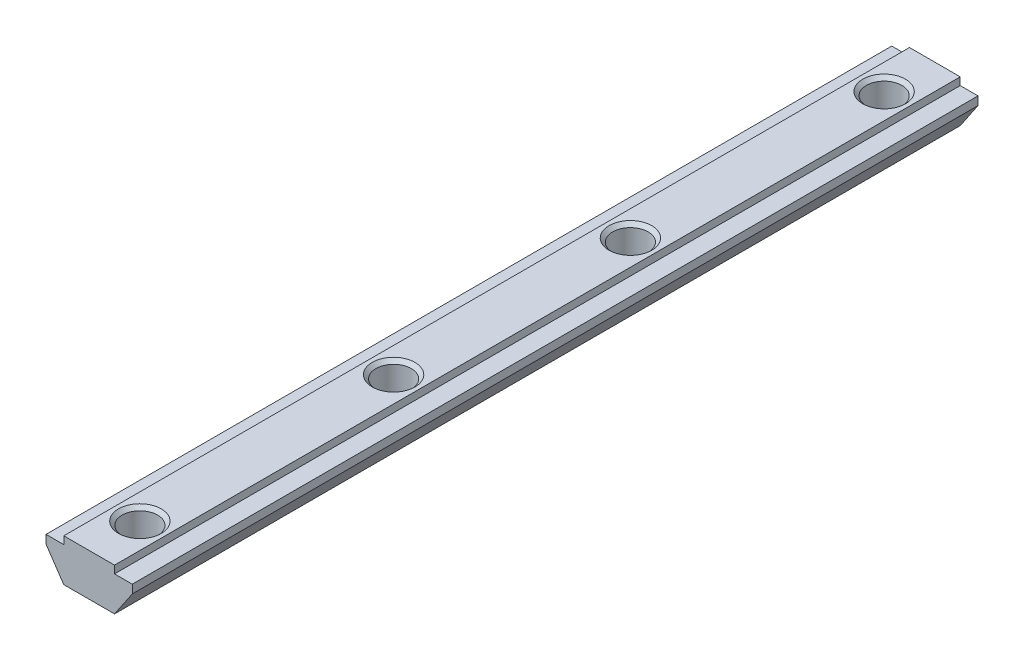
SolidWorks part; units mm, degrees
ref_plane "Спереди" through (0, 0, 0) normal (0, 0, 1) x (1, 0, 0)
ref_plane "Сверху" through (0, 0, 0) normal (0, 1, 0) x (1, 0, 0)
ref_plane "Справа" through (0, 0, 0) normal (1, 0, 0) x (0, 0, -1)
sketch "Эскиз1" plane through (0, 0, 0) normal (0, 0, 1) x (1, 0, 0)
  line L0 (3, 0) -> (-3, 0)
  line L1 (-3, 0) -> (-3, -0.9)
  line L2 (-3, -0.9) -> (-5.1, -0.9)
  line L3 (-5.1, -0.9) -> (-5.1, -1.9)
  line L4 (-5.1, -1.9) -> (-3, -5)
  line L5 (-3, -5) -> (3, -5)
  line L6 (0, -5) -> (0, 0) construction
  line L7 (5.1, -1.9) -> (3, -5)
  line L8 (5.1, -0.9) -> (5.1, -1.9)
  line L9 (3, -0.9) -> (5.1, -0.9)
  line L10 (3, 0) -> (3, -0.9)
  dimension "D1" = 6
  dimension "D2" = 10.2
  dimension "D3" = 5
  dimension "D4" = 4.1
  dimension "D5" = 1
extrude "Бобышка-Вытянуть1" add sketch "Эскиз1" along normal mid plane 100
hole_wizard "Отверстие обработанное метчиком M51" positions "Эскиз3" profile "Эскиз4" tap size "M5" standard "ISO" end condition through all
sketch "Эскиз3" plane through (0, 0, 0) normal (0, 1, 0) x (1, 0, 0)
  line L0 (0, -50) -> (0, -44)
  line L1 (3, -50) -> (-3, -50) construction
  line L2 (0, -44) -> (0, -14)
  line L4 (0, 50) -> (0, 44)
  line L5 (3, 50) -> (-3, 50) construction
  line L6 (0, 44) -> (0, 14)
  point P0 (0, 44)
  point P2 (0, 14)
  point P4 (0, -14)
  point P6 (0, -44)
  dimension "D1" = 6
  dimension "D2" = 30
sketch "Эскиз4" plane through (0, 0, -44) normal (1, 0, 0) x (0, 0, 1)
  line L0 (0, 0) -> (0, 5)
  line L1 (0, 5) -> (2.525, 5)
  line L2 (2.1, 4.575) -> (2.1, 0.425)
  line L3 (2.1, 0.425) -> (2.525, 0)
  line L5 (2.525, 0) -> (0, 0)
  line L6 (-2.1, 0.425) -> (-2.525, 0) construction
  line L7 (2.525, 5) -> (2.1, 4.575)
  line L8 (-2.525, 5) -> (-2.1, 4.575) construction
  line L11 (0, -6.35) -> (0, 107.95) construction
  dimension "Диаметр проходного сверла" = 4.2
  dimension "Глубина проходного сверла" = 5
  dimension "Диаметр передней зенковки" = 5.05
  dimension "Угол передней зенковки" = 90
  dimension "Диаметр задней зенковки" = 5.05
  dimension "Угол задней зенковки" = 90
cosmetic thread "Отверстие резьбы1" parameters "D2"=5
cosmetic thread "Отверстие резьбы2" parameters "D2"=5
cosmetic thread "Отверстие резьбы3" parameters "D2"=5
cosmetic thread "Отверстие резьбы4" parameters "D2"=5
